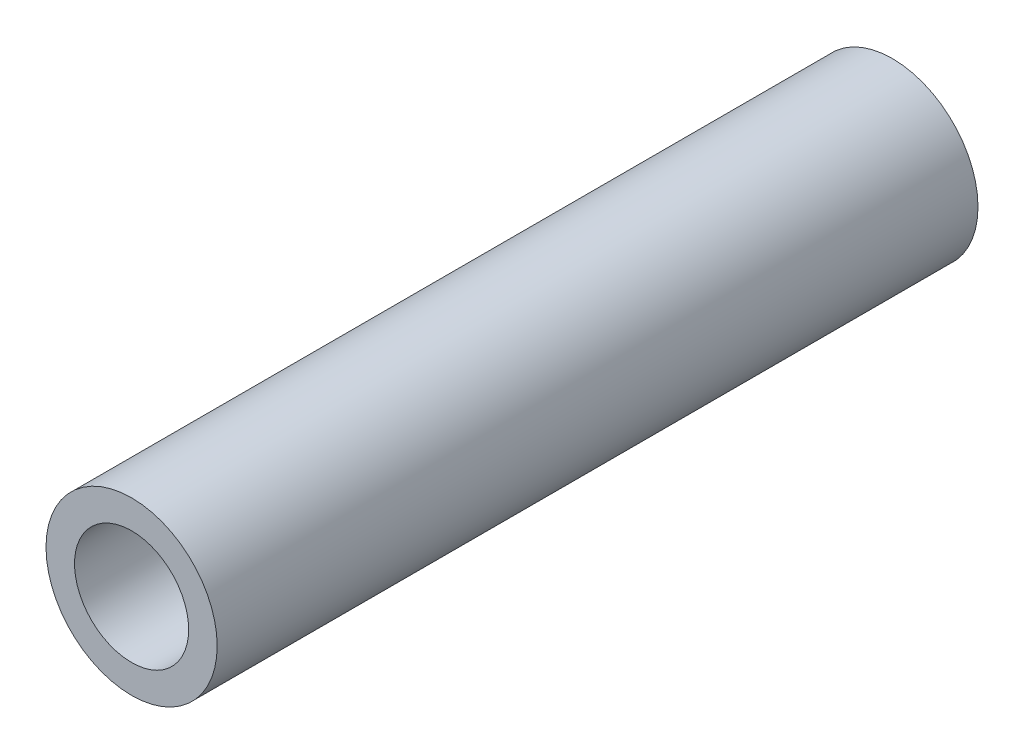
SolidWorks part; units mm, degrees
ref_plane "Front Plane" through (0, 0, 0) normal (0, 0, 1) x (1, 0, 0)
ref_plane "Top Plane" through (0, 0, 0) normal (0, 1, 0) x (1, 0, 0)
ref_plane "Right Plane" through (0, 0, 0) normal (1, 0, 0) x (0, 0, -1)
sketch "Sketch1" plane through (0, 0, 0) normal (0, 0, 1) x (1, 0, 0)
  circle A0 centre (0, 0) radius 6
  circle A1 centre (0, 0) radius 9
  dimension "D1" = 12
  dimension "D2" = 18
extrude "Main" add sketch "Sketch1" along normal blind 80
